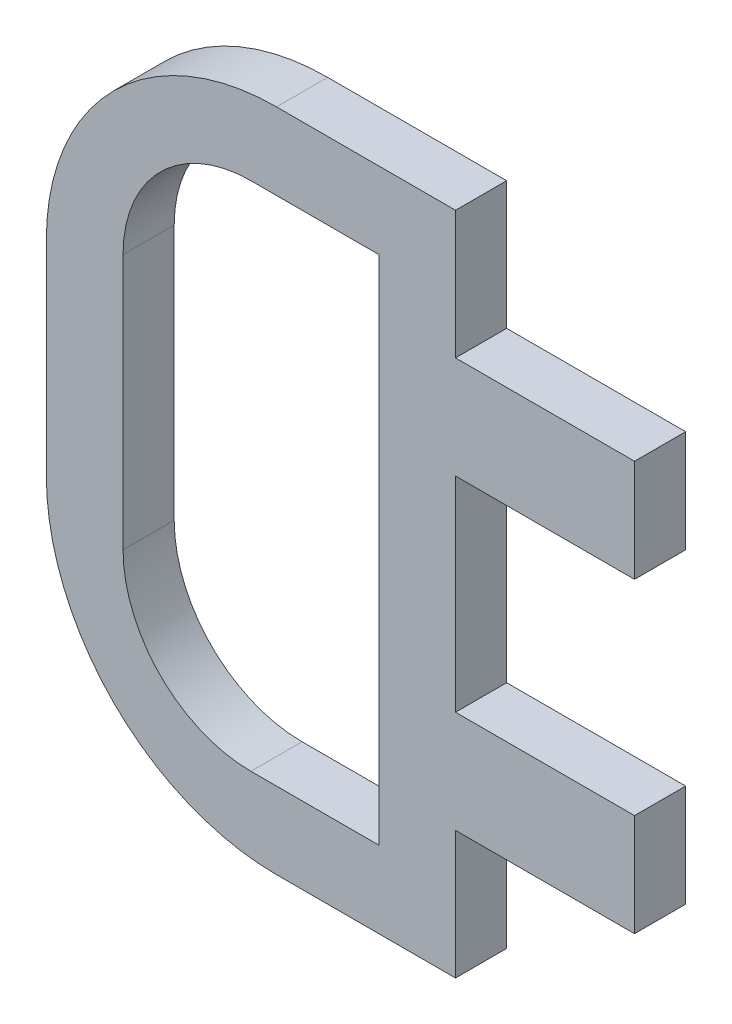
SolidWorks part; units mm, degrees
ref_plane "Plan de face" through (0, 0, 0) normal (0, 0, 1) x (1, 0, 0)
ref_plane "Plan de dessus" through (0, 0, 0) normal (0, 1, 0) x (1, 0, 0)
ref_plane "Plan de droite" through (0, 0, 0) normal (1, 0, 0) x (0, 0, -1)
sketch "Esquisse1" plane through (0, 0, 0) normal (0, 0, 1) x (1, 0, 0)
  line L1 (5, 65) -> (40, 65)
  line L2 (-40, 20) -> (-40, -20)
  line L3 (5, -65) -> (40, -65)
  line L4 (40, 65) -> (40, -65)
  line L5 (0, 50) -> (25, 50)
  line L6 (-25, 25) -> (-25, -25)
  line L7 (0, -50) -> (25, -50)
  line L8 (25, 50) -> (25, -50)
  arc A0 (-40, -20) -> (5, -65) centre (5, -20) ccw
  arc A1 (5, 65) -> (-40, 20) centre (5, 20) ccw
  arc A2 (-25, -25) -> (0, -50) centre (0, -25) ccw
  arc A3 (0, 50) -> (-25, 25) centre (0, 25) ccw
  point P7 (-40, -65)
  point P10 (-40, 65)
  dimension "D5" = 45
  dimension "D9" = 25
  dimension "D1" = 80
  dimension "D2" = 130
  dimension "D3" = 65
  dimension "D4" = 40
  dimension "D6" = 15
  dimension "D7" = 100
  dimension "D8" = 15
  dimension "D10" = 50
  dimension "D11" = 15
extrude "Boss.-Extru.1" add sketch "Esquisse1" along normal blind 10
sketch "Esquisse2" plane through (0, 0, 10) normal (0, 0, 1) x (1, 0, 0)
  line L0 (40, -65) -> (40, 65) construction
  line L1 (40, 40) -> (75, 40)
  line L2 (40, 40) -> (40, 20)
  line L3 (40, 20) -> (75, 20)
  line L4 (75, 40) -> (75, 20)
  line L5 (40, 65) -> (5, 65) construction
  line L6 (40, -20) -> (75, -20)
  line L7 (40, -20) -> (40, -40)
  line L8 (40, -40) -> (75, -40)
  line L9 (75, -20) -> (75, -40)
  dimension "D1" = 20
  dimension "D2" = 20
  dimension "D3" = 35
  dimension "D4" = 35
  dimension "D5" = 40
  dimension "D6" = 25
extrude "Boss.-Extru.2" add sketch "Esquisse2" against normal blind 10
equation "\"D3@Esquisse1\"=\"D2@Esquisse1\"/2"
equation "\"D4@Esquisse1\"=\"D1@Esquisse1\"/2"
